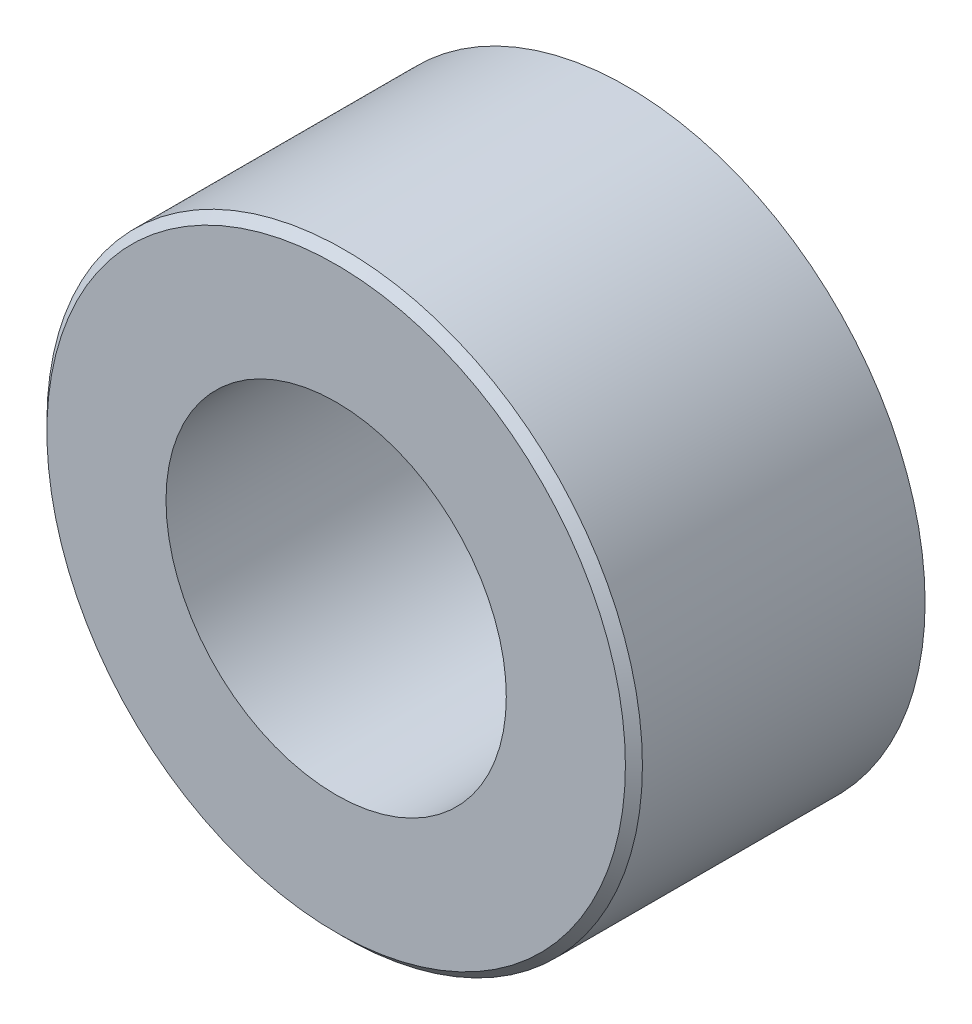
SolidWorks part; units mm, degrees
material "5052-O"
ref_plane "前基準面" through (0, 0, 0) normal (0, 0, 1) x (1, 0, 0)
ref_plane "上基準面" through (0, 0, 0) normal (0, 1, 0) x (1, 0, 0)
ref_plane "右基準面" through (0, 0, 0) normal (1, 0, 0) x (0, 0, -1)
sketch "Sketch1" plane through (0, 0, 0) normal (0, 0, 1) x (1, 0, 0)
  circle A0 centre (0, 0) radius 7
  circle A1 centre (0, 0) radius 4
  dimension "D1" = 14
  dimension "D2" = 8
extrude "Boss-Extrude1" add sketch "Sketch1" along normal blind 8
chamfer "Chamfer1" distance 0.2 angle 45 1 edges at (7, 0, 8)
chamfer "Chamfer2" distance 2 angle 30 1 edges at (7, 0, 0)
